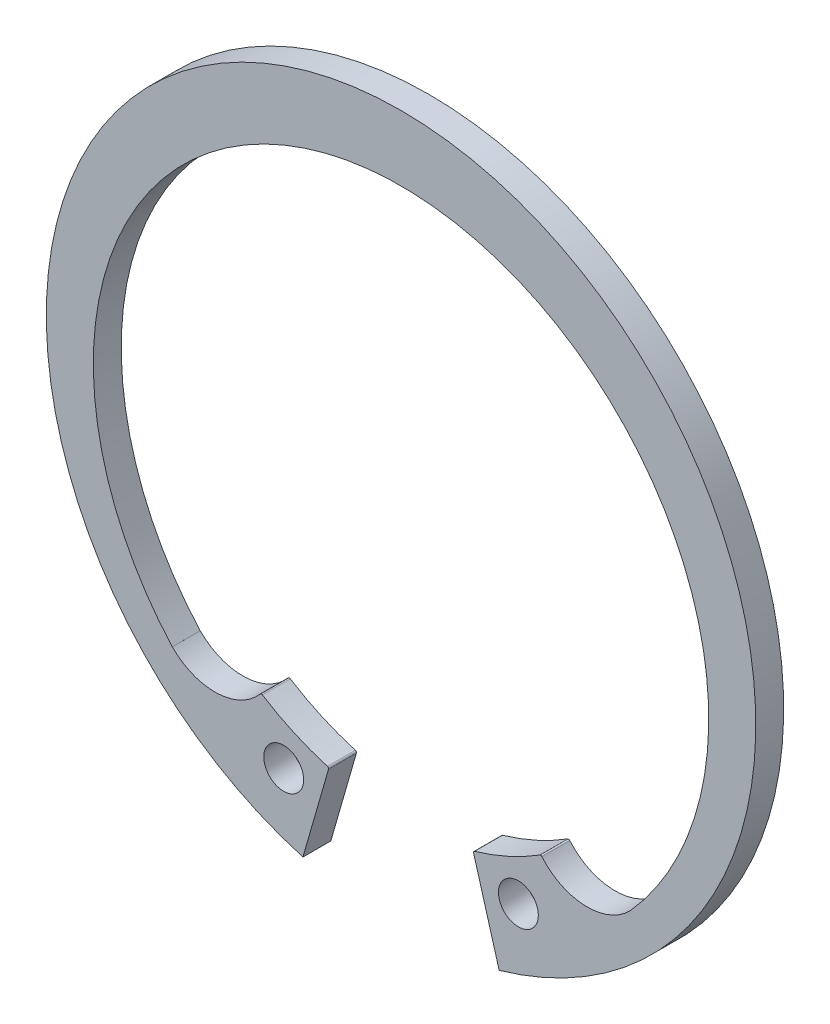
SolidWorks part; units mm, degrees
ref_plane "Plane1" through (0, 0, 0) normal (0, 0, 1) x (1, 0, 0)
ref_plane "Plane2" through (0, 0, 0) normal (0, 1, 0) x (1, 0, 0)
ref_plane "Plane3" through (0, 0, 0) normal (1, 0, 0) x (0, 0, -1)
sketch "Clipboard" plane through (0, 0, 0) normal (0, 0, 1) x (1, 0, 0)
  line L0 (0, 0) -> (4.1, 0)
  line L1 (0, 0) -> (0, 2.05)
  line L2 (0, 0) -> (0, -5.9)
  circle A0 centre (0, 0) radius 1.25
  circle A1 centre (0, 0) radius 21
  dimension "HoleDia" = 2.5
  dimension "BoreDia" = 42
  dimension "LargeSection" = 4.1
  dimension "SmallSection" = 2.05
  dimension "LugSection" = 5.9
sketch "BodySke" plane through (0, 0, 0) normal (0, 0, 1) x (1, 0, 0)
  line L0 (-1.5431, 0) -> (1.5431, 0) construction
  line L1 (0, 0) -> (0, 18.15) construction
  line L2 (6.1547, -21.3818) -> (5.1256, -17.8067)
  line L3 (-6.1547, -21.3818) -> (-5.1256, -17.8067)
  line L4 (0, 0) -> (13.5796, -17.6255) construction
  line L5 (0, 0) -> (-13.5796, -17.6255) construction
  line L6 (-7.0141, -15.9623) -> (-7.7057, -18.3648) construction
  line L7 (7.1523, -16.4422) -> (7.5675, -17.8848) construction
  arc A0 (-5.1256, -17.8067) -> (-9.1342, -15.661) centre (-7.3599, -17.1635) ccw
  arc A1 (9.1342, -15.661) -> (5.1256, -17.8067) centre (7.3599, -17.1635) ccw
  arc A2 (12.3284, -16.0015) -> (-12.3284, -16.0015) centre (0, -1.151) ccw construction
  arc A3 (6.1547, -21.3818) -> (-6.1547, -21.3818) centre (0, 0) ccw
  circle A4 centre (7.3599, -17.1635) radius 1.25
  circle A5 centre (-7.3599, -17.1635) radius 1.25
  circle A6 centre (7.3599, -17.1635) radius 2.325 construction
  arc A7 (12.4024, -15.9399) -> (-12.4024, -15.9399) centre (0, -1.151) ccw
  arc A8 (-7.3599, -17.1635) -> (7.3599, -17.1635) centre (0, 0) ccw construction
  arc A9 (-12.4024, -15.9399) -> (-9.1342, -15.661) centre (-10.9084, -14.1584) ccw
  arc A10 (9.1342, -15.661) -> (12.4024, -15.9399) centre (10.9084, -14.1584) ccw
  dimension "GrooveDia" = 44.5
  dimension "TipRad" = 2.325
  dimension "HoleOffsetRad" = 18.675
  dimension "HoleDia" = 2.5
  dimension "FilletRad" = 2.325
  dimension "LargeRad" = 18.15
  dimension "SmallRad" = 20.2
  dimension "SmallAngle" = 75.225
  dimension "GapAngle" = 32.117
extrude "Body" add sketch "BodySke" against normal blind 1.75
sketch "ModLugSke" plane through (0, 0, 0) normal (0, 0, 1) x (1, 0, 0)
  line L0 (6.1547, -21.3818) -> (4.5503, -15.8078)
  line L1 (-6.1547, -21.3818) -> (-4.5503, -15.8078)
  line L2 (11.6776, -11.4436) -> (15.8915, -15.5731) construction
  line L3 (-11.6776, -11.4436) -> (-15.8915, -15.5731) construction
  line L4 (-6.1547, -21.3818) -> (-5.1256, -17.8067) construction
  line L5 (5.1256, -17.8067) -> (6.1547, -21.3818) construction
  line L6 (0, 0) -> (0, -18.0732) construction
  line L7 (14.3451, -14.0577) -> (15.8915, -15.5731)
  line L8 (-15.8915, -15.5731) -> (-14.3451, -14.0577)
  arc A0 (6.1547, -21.3818) -> (15.8915, -15.5731) centre (0, 0) ccw
  arc A1 (-8.7018, -13.842) -> (-4.6181, -15.6842) centre (0, 0) ccw
  arc A2 (6.1547, -21.3818) -> (-6.1547, -21.3818) centre (0, 0) ccw construction
  arc A3 (9.1342, -15.661) -> (5.1256, -17.8067) centre (7.3599, -17.1635) ccw construction
  arc A4 (-8.7018, -13.842) -> (-8.8313, -13.8619) centre (-8.7551, -13.9266) ccw
  arc A5 (-14.3451, -14.0577) -> (-8.8313, -13.8619) centre (-11.6776, -11.4436) ccw
  arc A6 (12.4024, -15.9399) -> (-12.4024, -15.9399) centre (0, -1.151) ccw construction
  arc A7 (8.8313, -13.8619) -> (14.3451, -14.0577) centre (11.6776, -11.4436) ccw
  arc A8 (4.6181, -15.6842) -> (8.7018, -13.842) centre (0, 0) ccw
  arc A9 (-15.8915, -15.5731) -> (-6.1547, -21.3818) centre (0, 0) ccw
  circle A10 centre (-7.3599, -17.1635) radius 1.25
  circle A11 centre (-7.3599, -17.1635) radius 1.25 construction
  circle A12 centre (7.3599, -17.1635) radius 1.25
  circle A13 centre (7.3599, -17.1635) radius 1.25 construction
  arc A14 (-4.6181, -15.6842) -> (-4.5503, -15.8078) centre (-4.6464, -15.7802) cw
  arc A15 (4.6181, -15.6842) -> (4.5503, -15.8078) centre (4.6464, -15.7802) ccw
  arc A16 (8.7018, -13.842) -> (8.8313, -13.8619) centre (8.7551, -13.9266) cw
  point P43 (4.5227, -15.712)
  dimension "D1" = 0.1
  dimension "LugAng" = 64.312
extrude "ModLug" add sketch "ModLugSke" against normal through all
sketch "UnlSke" [suppressed] plane through (0, 0, 0) normal (0, 0, 1) x (1, 0, 0)
  line L0 (2.1178, -8.3352) -> (3.2259, -12.6966)
  line L1 (-2.1178, -8.3352) -> (-3.2259, -12.6966)
  line L2 (-3.2259, -12.6966) -> (-2.1422, -8.4315) construction
  line L3 (2.1422, -8.4315) -> (3.2259, -12.6966) construction
  arc A0 (2.1178, -8.3352) -> (-2.1178, -8.3352) centre (0, 0) ccw
  arc A1 (3.2259, -12.6966) -> (-3.2259, -12.6966) centre (0, 0) ccw
  arc A2 (3.2259, -12.6966) -> (-3.2259, -12.6966) centre (0, 0) ccw construction
  circle A4 centre (-4.4431, -9.5688) radius 1
  circle A5 centre (4.4431, -9.5688) radius 1
  circle A6 centre (4.4431, -9.5688) radius 1 construction
  circle A7 centre (-4.4431, -9.5688) radius 1 construction
  arc A8 (2.2134, -8.3103) -> (4.9183, -7.0548) centre (0, 0) ccw construction
extrude "Unlug" [suppressed] add sketch "UnlSke" against normal through all
equation "' \"BoreDia@Clipboard\" = 8"
equation "' \"Thickness@Body\" = 0.8"
equation "' \"GrooveDia@BodySke\" = 8.4"
equation "' \"LugSection@Clipboard\" = 2.4"
equation "' \"LargeSection@Clipboard\" = 1.1"
equation "' \"HoleDia@Clipboard\" = 1.0"
equation "' \"BoreDia@Clipboard\" = 25"
equation "' \"Thickness@Body\" = 1.2"
equation "' \"GrooveDia@BodySke\" = 26.2"
equation "' \"LugSection@Clipboard\" = 4.5"
equation "' \"LargeSection@Clipboard\" = 2.7"
equation "' \"HoleDia@Clipboard\" = 2"
equation "\"SmallSection@Clipboard\" = \"LargeSection@Clipboard\" * 0.5"
equation "\"TipRad@BodySke\" = (\"LugSection@Clipboard\" - (\"GrooveDia@BodySke\" / 2  -  \"BoreDia@Clipboard\" / 2 ) ) / 2"
equation "\"HoleOffsetRad@BodySke\" = (\"GrooveDia@BodySke\" / 2) - \"LugSection@Clipboard\"  + \"TipRad@BodySke\""
equation "\"LargeRad@BodySke\" =  \"GrooveDia@BodySke\" / 2 -  \"LargeSection@Clipboard\""
equation "\"SmallRad@BodySke\" =  \"GrooveDia@BodySke\" / 2 -  \"SmallSection@Clipboard\""
equation "\"HoleDia@BodySke\" =  \"HoleDia@Clipboard\""
equation "\"FilletRad@BodySke\" = \"TipRad@BodySke\" * 1.0"
equation "\"GapAngle@BodySke\" = 360 - 0.965 * 360 * ( \"BoreDia@Clipboard\" /  \"GrooveDia@BodySke\")"
equation "\"LugAng@ModLugSke\" = \"GapAngle@BodySke\"  + 2 * 360 * (\"LugSection@Clipboard\" / (\"BoreDia@Clipboard\" * 3.1416))"
